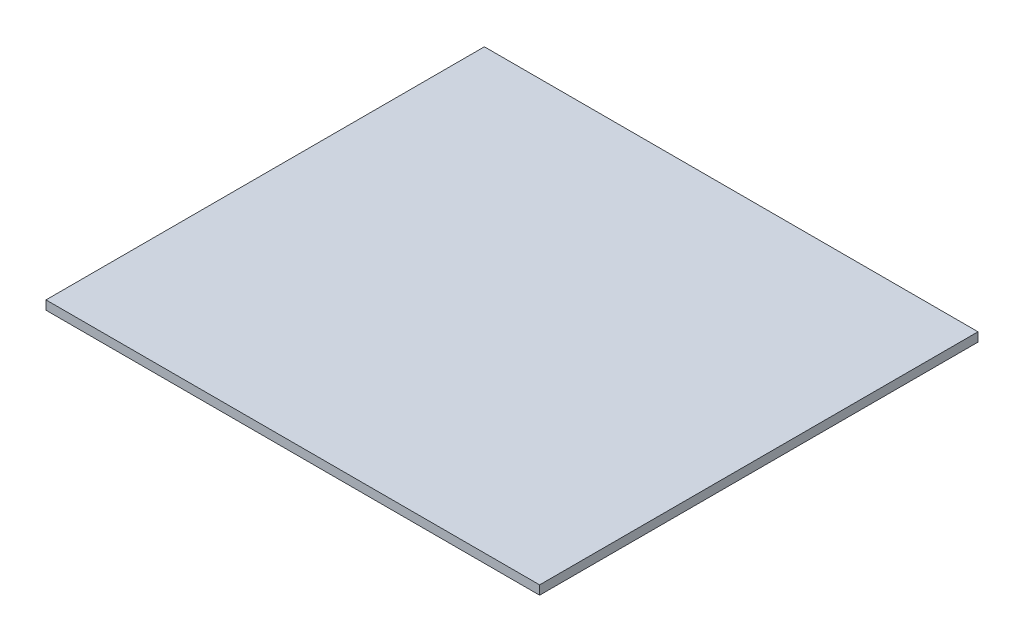
SolidWorks part; units mm, degrees
ref_plane "Front Plane" through (0, 0, 0) normal (0, 0, 1) x (1, 0, 0)
ref_plane "Top Plane" through (0, 0, 0) normal (0, 1, 0) x (1, 0, 0)
ref_plane "Right Plane" through (0, 0, 0) normal (1, 0, 0) x (0, 0, -1)
sketch "Sketch1" plane through (0, 0, 0) normal (0, 1, 0) x (1, 0, 0)
  line L1 (-35.75, 31.75) -> (35.75, 31.75)
  line L2 (-35.75, 31.75) -> (-35.75, -31.75)
  line L3 (-35.75, -31.75) -> (35.75, -31.75)
  line L4 (35.75, 31.75) -> (35.75, -31.75)
  line L5 (-35.75, 31.75) -> (35.75, -31.75) construction
  line L6 (-35.75, -31.75) -> (35.75, 31.75) construction
  point P0 (0, 0)
  dimension "D1" = 63.5
  dimension "D2" = 71.5
extrude "Boss-Extrude1" add sketch "Sketch1" along normal blind 1.3
